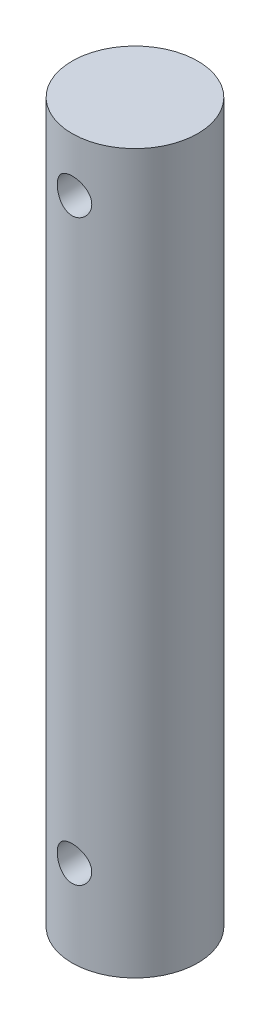
SolidWorks part; units mm, degrees
ref_plane "Front" through (0, 0, 0) normal (0, 0, 1) x (1, 0, 0)
ref_plane "Top" through (0, 0, 0) normal (0, 1, 0) x (1, 0, 0)
ref_plane "Right" through (0, 0, 0) normal (1, 0, 0) x (0, 0, -1)
sketch "Sketch1" plane through (0, 0, 0) normal (0, 1, 0) x (1, 0, 0)
  circle A0 centre (0, 0) radius 5.5562
  dimension "D1" = 11.1125
extrude "Boss-Extrude1" add sketch "Sketch1" along normal blind 63.5
ref_plane "Plane1" through (0, 0, 5.5562) normal (0, 0, 1) x (1, 0, 0)
hole_wizard "#31 (0.12) Diameter Hole1" positions "Sketch2" profile "Sketch3" hole size "#31" standard "ANSI Inch" end condition through all
sketch "Sketch2" plane through (0, 0, 5.5562) normal (0, 0, 1) x (1, 0, 0)
  line L0 (5.5562, 63.5) -> (-5.5562, 63.5) construction
  line L1 (5.5562, 63.5) -> (-5.5562, 63.5)
  line L2 (0, 58.7375) -> (0, 63.5)
  line L4 (-5.5562, 0) -> (5.5562, 0) construction
  line L5 (-5.5562, 0) -> (5.5562, 0)
  line L7 (0, 7.62) -> (0, 0)
  point P0 (0, 58.7375)
  point P2 (0, 7.62)
  dimension "D1" = 4.7625
  dimension "D2" = 7.62
sketch "Sketch3" plane through (0, 58.7375, 5.5562) normal (1, 0, 0) x (0, -1, 0)
  line L0 (0, 0) -> (0, 11.1125)
  line L1 (0, 11.1125) -> (1.524, 11.1125)
  line L2 (1.524, 11.1125) -> (1.524, 0)
  line L5 (1.524, 0) -> (0, 0)
  line L11 (0, -6.35) -> (0, 107.95) construction
  dimension "Thru Hole Dia." = 3.048
  dimension "Thru Hole Depth" = 11.1125
